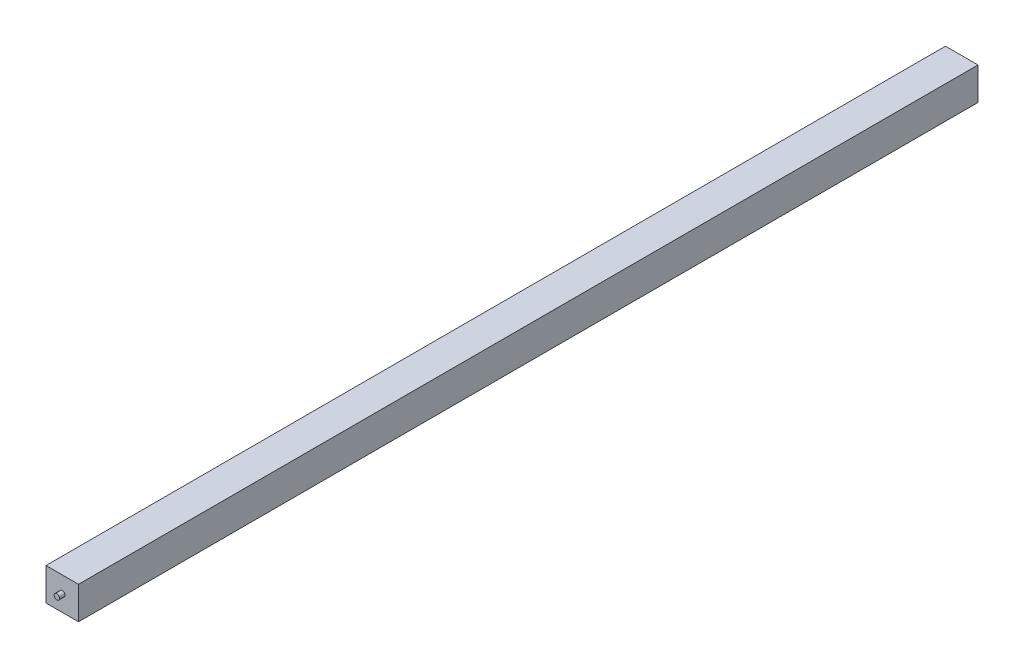
SolidWorks part; units mm, degrees
ref_plane "Front Plane" through (0, 0, 0) normal (0, 0, 1) x (1, 0, 0)
ref_plane "Top Plane" through (0, 0, 0) normal (0, 1, 0) x (1, 0, 0)
ref_plane "Right Plane" through (0, 0, 0) normal (1, 0, 0) x (0, 0, -1)
sketch "Sketch1" plane through (0, 0, 0) normal (1, 0, 0) x (0, 0, -1)
  line L0 (0, 0) -> (830, 0)
  line L1 (830, 0) -> (830, 30)
  line L2 (830, 30) -> (0, 30)
  line L3 (0, 30) -> (0, 0)
  dimension "D1" = 830
  dimension "D2" = 30
extrude "Boss-Extrude1" add sketch "Sketch1" along normal mid plane 30
sketch "Sketch3" plane through (0, 0, -830) normal (0, 0, -1) x (-1, 0, 0)
  line L0 (15, 0) -> (15, 30) construction
  line L1 (-15, 0) -> (15, 0) construction
  circle A0 centre (0, 15) radius 2.5
  dimension "D1" = 5
  dimension "D3" = 15
  dimension "D2" = 15
sketch "Sketch4" plane through (0, 0, 0) normal (0, 0, 1) x (1, 0, 0)
  line L1 (15, 30) -> (-15, 30) construction
  circle A0 centre (0, 15) radius 2.5
  dimension "D1" = 5
  dimension "D2" = 15
extrude "Boss-Extrude2" add sketch "Sketch3" along normal mid plane 10
extrude "Boss-Extrude3" add sketch "Sketch4" along normal mid plane 10
